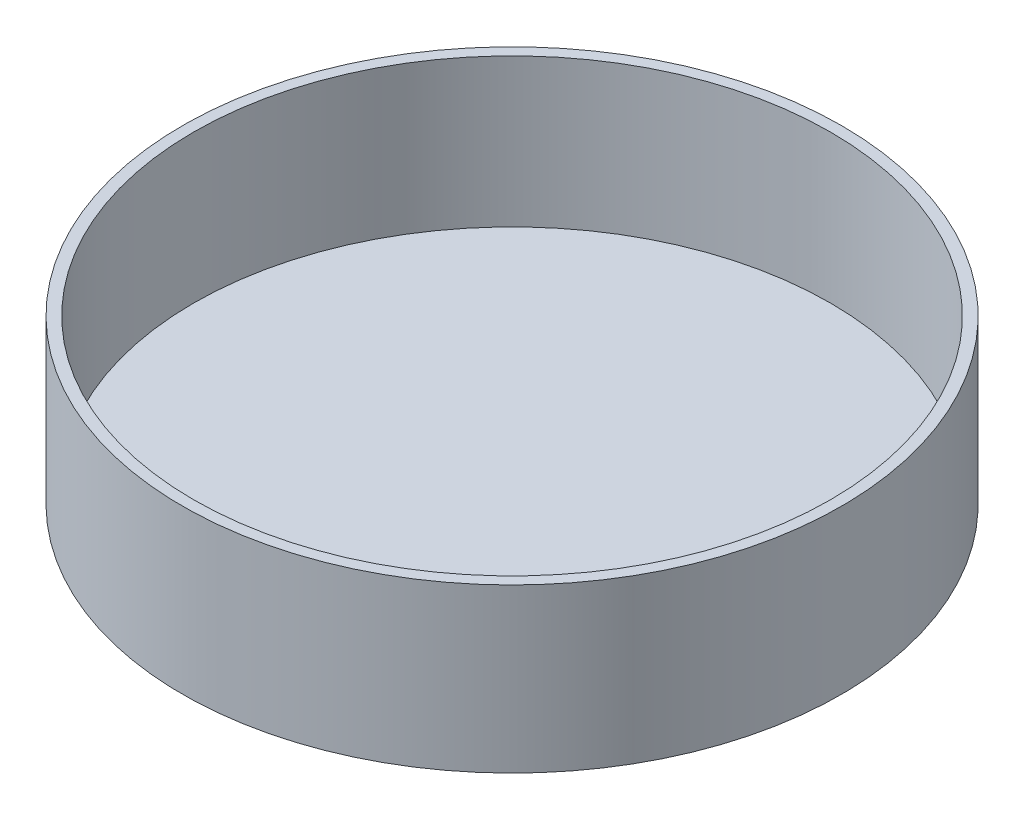
SolidWorks part; units mm, degrees
ref_plane "Front" through (0, 0, 0) normal (0, 0, 1) x (1, 0, 0)
ref_plane "Top" through (0, 0, 0) normal (0, 1, 0) x (1, 0, 0)
ref_plane "Right" through (0, 0, 0) normal (1, 0, 0) x (0, 0, -1)
sketch "Sketch1" plane through (0, 0, 0) normal (1, 0, 0) x (0, 0, -1)
  line L0 (0, 0) -> (-141.2875, 0)
  line L1 (-141.2875, 0) -> (-141.2875, 69.85)
  line L2 (-141.2875, 69.85) -> (-136.525, 69.85)
  line L3 (-136.525, 69.85) -> (-136.525, 6.35)
  line L4 (-136.525, 6.35) -> (0, 6.35)
  line L5 (0, 6.35) -> (0, 0)
  line L6 (0, -45.6337) -> (0, 123.0648) construction
  dimension "D1" = 273.05
  dimension "D2" = 4.7625
  dimension "D3" = 69.85
  dimension "D4" = 63.5
revolve "Revolve1" add sketch "Sketch1" angle 360 about L6
